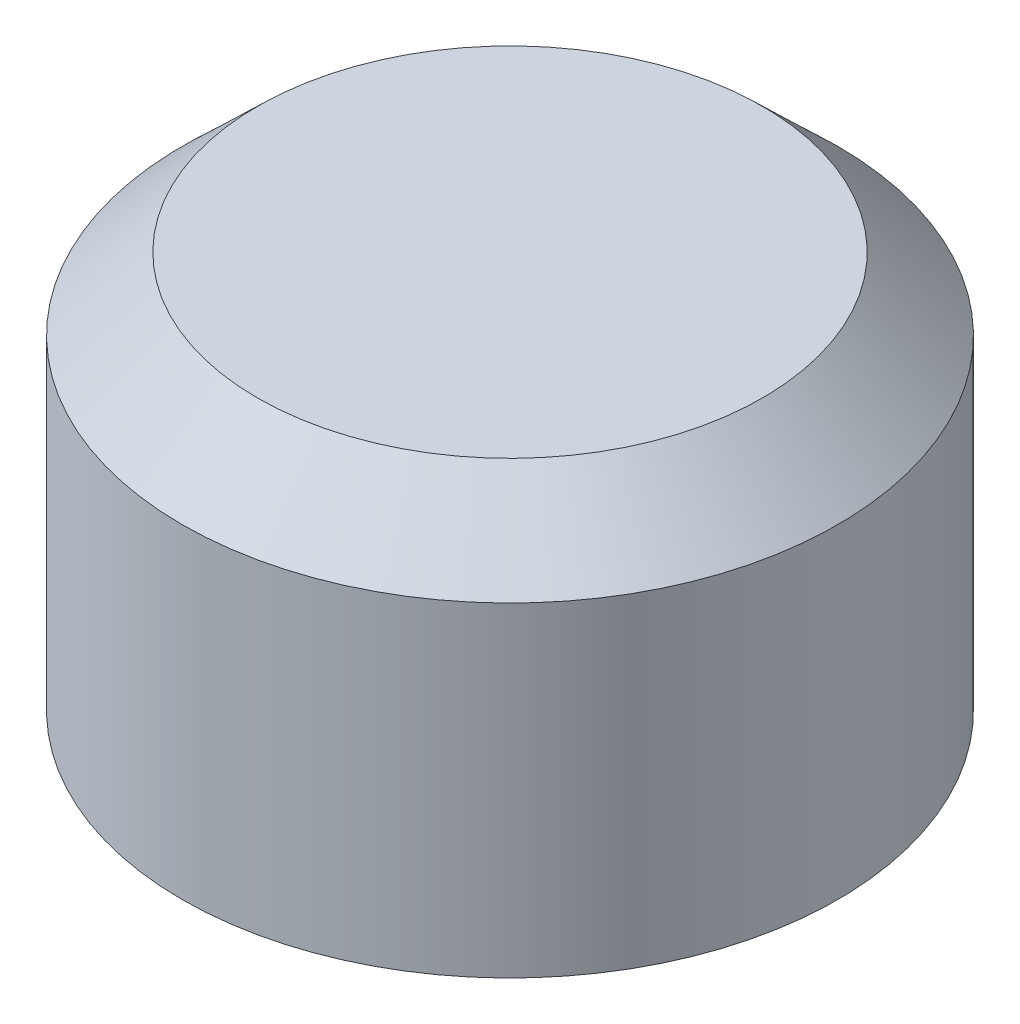
SolidWorks part; units mm, degrees
ref_plane "Front Plane" through (0, 0, 0) normal (0, 0, 1) x (1, 0, 0)
ref_plane "Top Plane" through (0, 0, 0) normal (0, 1, 0) x (1, 0, 0)
ref_plane "Right Plane" through (0, 0, 0) normal (1, 0, 0) x (0, 0, -1)
sketch "Sketch1" plane through (0, 0, 0) normal (0, 0, 1) x (1, 0, 0)
  line L0 (-2438.4, 0) -> (-2438.4, 2753.721)
  line L1 (-2438.4, 2753.721) -> (-2118.721, 3073.4)
  line L2 (-2118.721, 3073.4) -> (-1190.8772, 3073.4)
  line L3 (-1190.8772, 3073.4) -> (-914.4, 2796.9228)
  line L4 (-914.4, 2796.9228) -> (-914.4, 2074)
  line L6 (-939.8, 2074) -> (-939.8, 2786.4018)
  line L7 (-939.8, 2786.4018) -> (-1201.3982, 3048)
  line L8 (-1201.3982, 3048) -> (-2108.2, 3048)
  line L9 (-2108.2, 3048) -> (-2413, 2743.2)
  line L10 (-2413, 2743.2) -> (-2413, 0)
  line L11 (-2413, 0) -> (-2438.4, 0)
  line L12 (-914.4, 2074) -> (-766.9906, 1523.8607)
  line L13 (-766.9906, 1523.8607) -> (-792.3906, 1523.8607)
  line L14 (-939.8, 2074) -> (-792.3906, 1523.8607)
  point P2 (-939.8, 2074)
  point P14 (-914.4, 2074)
  dimension "D1" = 25.4
  dimension "D3" = 2743.2
  dimension "D4" = 304.8
  dimension "D5" = 304.8
  dimension "D6" = 25.4
  dimension "D8" = 25.4
  dimension "D9" = 25.4
  dimension "D11" = 2438.4
  dimension "D13" = 15
  dimension "D14" = 25.4
sketch "Sketch2" plane through (0, 0, 0) normal (0, 0, 1) x (1, 0, 0)
  line L0 (-2743.2, 0) -> (-2768.6, 0)
  line L1 (-2768.6, 0) -> (-2768.6, 2743.2)
  line L2 (-2743.2, 0) -> (-2743.2, 2732.3741)
  line L3 (-2743.2, 2732.3741) -> (-2123.3813, 3327.4)
  line L4 (-2123.3813, 3327.4) -> (0, 3327.4)
  line L5 (0, 3327.4) -> (0, 3352.8)
  line L6 (0, 3352.8) -> (-2133.6, 3352.8)
  line L7 (-2133.6, 3352.8) -> (-2768.6, 2743.2)
  dimension "D1" = 2743.2
  dimension "D2" = 2133.6
  dimension "D3" = 25.4
  dimension "D4" = 25.4
  dimension "D5" = 304.8
  dimension "D6" = 609.6
  dimension "D7" = 25.4
ref_axis "Axis1" through (0, 3520.44, 0) along (0, -1, 0)
revolve "Revolve1" add sketch "Sketch1" angle 360 about axis through (0, 3520.44, 0) along (0, -1, 0)
revolve "Revolve2" add sketch "Sketch2" angle 360 about axis through (0, 3520.44, 0) along (0, -1, 0)
